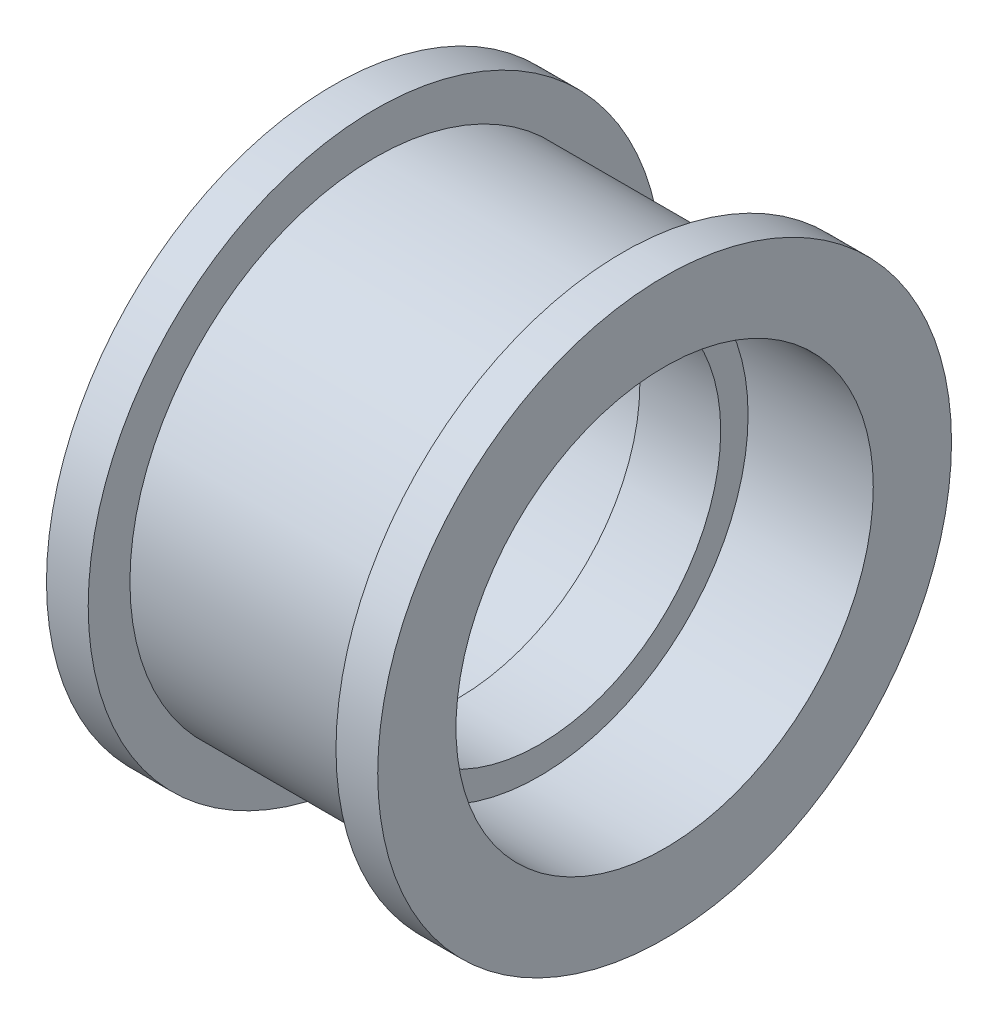
SolidWorks part; units mm, degrees
material "Delrin 2700 NC010, Low Viscosity Acetal Copolymer (SS)"
ref_plane "Front Plane" through (0, 0, 0) normal (0, 0, 1) x (1, 0, 0)
ref_plane "Top Plane" through (0, 0, 0) normal (0, 1, 0) x (1, 0, 0)
ref_plane "Right Plane" through (0, 0, 0) normal (1, 0, 0) x (0, 0, -1)
sketch "Sketch1" plane through (0, 0, 0) normal (0, 0, 1) x (1, 0, 0)
  line L0 (1.55, 6.95) -> (-1.55, 6.95)
  line L1 (-1.55, 6.95) -> (-1.55, 8)
  line L2 (-1.55, 8) -> (-6.35, 8)
  line L3 (-6.35, 8) -> (-6.35, 11)
  line L4 (-6.35, 11) -> (-4.75, 11)
  line L5 (-4.75, 9.4) -> (4.75, 9.4)
  line L6 (0, 9.4) -> (0, 6.95) construction
  line L7 (-4.75, 11) -> (-4.75, 9.4)
  line L8 (6.35, 8) -> (6.35, 11)
  line L9 (1.55, 8) -> (6.35, 8)
  line L10 (1.55, 6.95) -> (1.55, 8)
  line L11 (0, 0) -> (-12.6359, 0) construction
  line L12 (4.75, 11) -> (4.75, 9.4)
  line L13 (6.35, 11) -> (4.75, 11)
  dimension "D1" = 1.6
  dimension "8.64" = 13.9
  dimension "D2" = 16
  dimension "D3" = 18.8
  dimension "D4" = 3.1
  dimension "D5" = 22
  dimension "D6" = 12.7
revolve "Revolve1" add sketch "Sketch1" angle 360 about L11
